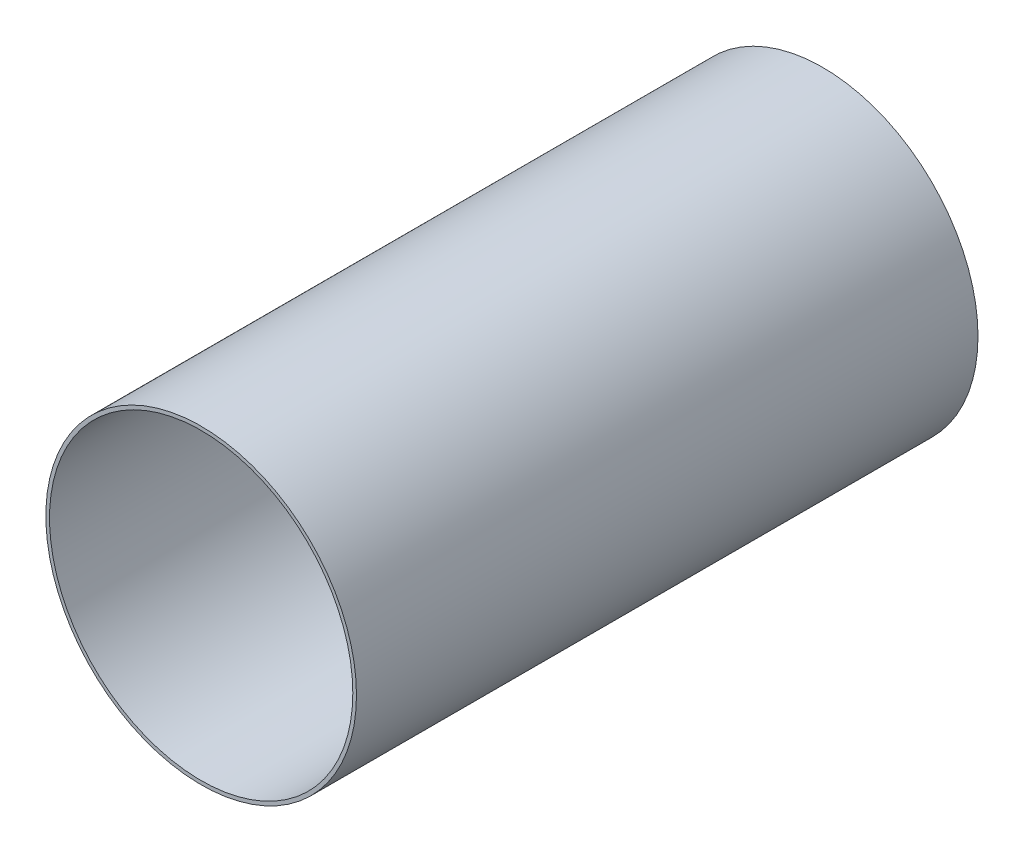
SolidWorks part; units mm, degrees
ref_plane "Front Plane" through (0, 0, 0) normal (0, 0, 1) x (1, 0, 0)
ref_plane "Top Plane" through (0, 0, 0) normal (0, 1, 0) x (1, 0, 0)
ref_plane "Right Plane" through (0, 0, 0) normal (1, 0, 0) x (0, 0, -1)
sketch "Sketch1" plane through (0, 0, 0) normal (0, 0, 1) x (1, 0, 0)
  circle A0 centre (0, 0) radius 63.4746
  circle A1 centre (0, 0) radius 61.976
  dimension "D1" = 123.952
  dimension "D2" = 126.9492
extrude "Boss-Extrude1" add sketch "Sketch1" along normal mid plane 254
equation "\"AIRFRAME_OD\"= 5.15in"
equation "\"AIRFRAME_ID\"= 5.00in"
equation "\"FLAT_T\"= 0.125in"
equation "\"NOSE_EXP_L\"= 27in"
equation "\"NOSE_SHOULDER_L\"= 5in"
equation "\"MAIN_L\"= 30in"
equation "\"RECO_COUP_L\"= 10in"
equation "\"RECO_SWITCH_L\"= 2in"
equation "\"DROGUE_L\"= 20in"
equation "\"ATS_FORE_COUP_L\"= 5.5in"
equation "\"ATS_AFT_COUP_L\"= 4.5in"
equation "\"LOWER_L\"= 30in"
equation "\"FIN_N\"= 4"
equation "\"CR_AFT_X\"= 0.5in"
equation "\"CR_FORE_X\"= 9.25in"
equation "\"D1@Sketch1\"=\"COUPLER_ID\""
equation "\"D2@Sketch1\"=\"COUPLER_OD\""
equation "\"D1@Boss-Extrude1\"=\"RECO_COUP_L\""
equation "\"FIN_ROOT\"= 8in"
equation "\"FIN_X\"= 0.75in"
equation "\"MOTOR_OD\"= 3.091in"
equation "\"MOTOR_ID\"= 3.00in"
equation "\"COUPLER_OD\"= 4.998in"
equation "\"COUPLER_ID\"= 4.88in"
equation "\"RECO_ROD_X\"= 3.5in"
equation "\"ATS_ROD_X\"= 3in"
equation "\"MOTOR_L\"= 14in"
equation "\"MOTOR_LOWER_X\"= 2in"
